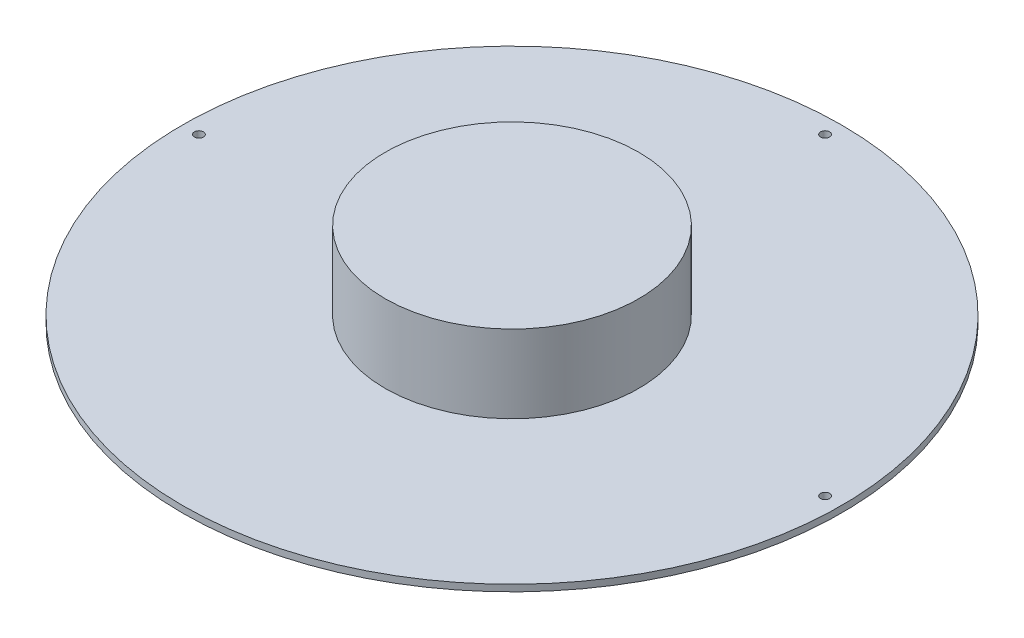
SolidWorks part; units mm, degrees
ref_plane "Front Plane" through (0, 0, 0) normal (0, 0, 1) x (1, 0, 0)
ref_plane "Top Plane" through (0, 0, 0) normal (0, 1, 0) x (1, 0, 0)
ref_plane "Right Plane" through (0, 0, 0) normal (1, 0, 0) x (0, 0, -1)
sketch "Sketch1" plane through (0, 0, 0) normal (0, 1, 0) x (1, 0, 0)
  circle A0 centre (0, 0) radius 80
extrude "Boss-Extrude1" add sketch "Sketch1" along normal blind 1.6
sketch "Sketch2" plane through (0, 1.6, 0) normal (0, 1, 0) x (1, 0, 0)
  circle A0 centre (0, 0) radius 2.3
extrude "Cut-Extrude1" cut sketch "Sketch2" against normal blind 1.6
hole_wizard "M2 Clearance Hole2" positions "Sketch7" profile "Sketch8" hole size "M2" standard "ISO"
sketch "Sketch7" plane through (0, 1.6, 0) normal (0, 1, 0) x (1, 0, 0)
  point P0 (0, 76)
  point P2 (76, 0)
  point P6 (-76, 0)
  point P10 (0, 0)
  dimension "D1" = 76
  dimension "D2" = 76
  dimension "D4" = 76
sketch "Sketch8" plane through (0, 1.6, -76) normal (1, 0, 0) x (0, 0, 1)
  line L0 (0, 0) -> (0, 6.6609)
  line L1 (0, 6.6609) -> (1.1, 6)
  line L2 (1.1, 6) -> (1.1, 0)
  line L5 (1.1, 0) -> (0, 0)
  line L10 (0, 6.6609) -> (-1.1, 6) construction
  line L11 (0, -6.35) -> (0, 107.95) construction
  dimension "Hole Dia." = 2.2
  dimension "Hole Depth" = 6
  dimension "Drill Angle" = 118
sketch "Sketch9" plane through (0, 1.6, 0) normal (0, 1, 0) x (1, 0, 0)
  circle A0 centre (0, 0) radius 30.8
extrude "Boss-Extrude2" add sketch "Sketch9" along normal blind 18.86
sketch "Sketch10" plane through (0, 1.6, 0) normal (0, -1, 0) x (1, 0, 0)
  circle A0 centre (0, 0) radius 1.5
extrude "Boss-Extrude3" add sketch "Sketch10" along normal blind 4
sketch "Sketch11" plane through (0, -2.4, 0) normal (0, -1, 0) x (1, 0, 0)
  circle A0 centre (0, 0) radius 0.7
extrude "Boss-Extrude4" add sketch "Sketch11" along normal blind 3.8
